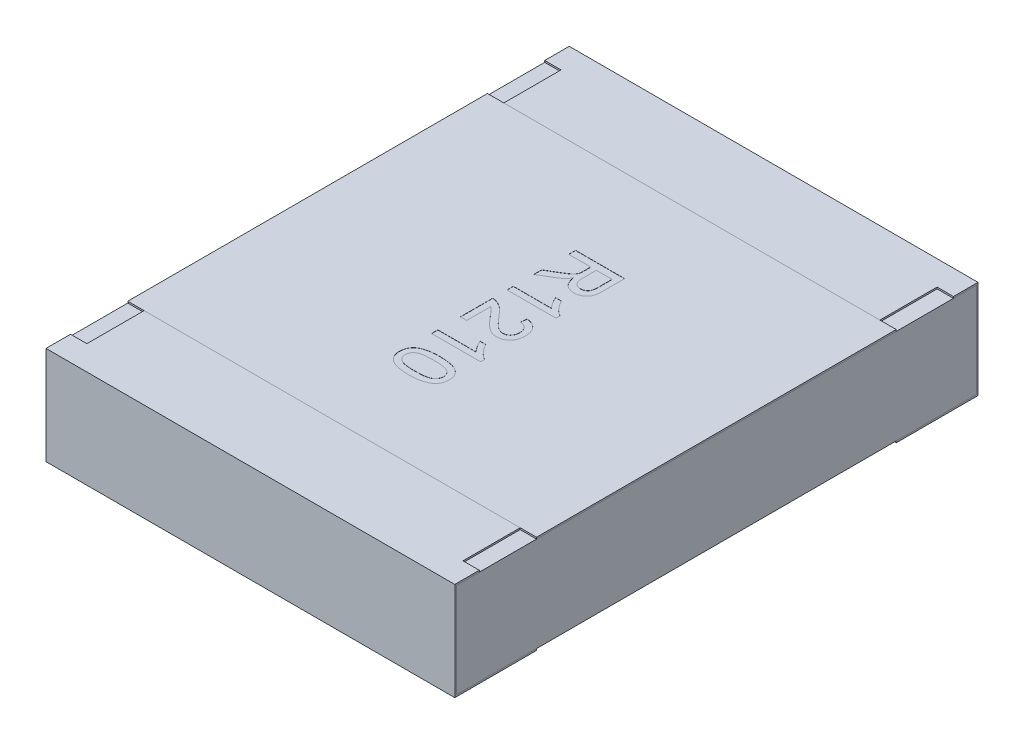
SolidWorks part; units mm, degrees
ref_plane "Front Plane" through (0, 0, 0) normal (0, 0, 1) x (1, 0, 0)
ref_plane "Top Plane" through (0, 0, 0) normal (0, 1, 0) x (1, 0, 0)
ref_plane "Right Plane" through (0, 0, 0) normal (1, 0, 0) x (0, 0, -1)
sketch "Sketch4" plane through (0, 0, 0) normal (1, 0, 0) x (0, 0, -1)
  line L0 (0, 0.1169) -> (0, -0.0721) construction
  line L1 (-1.6, 0) -> (0.3788, 0) construction
  line L2 (-1.6, 0.3) -> (-1.6, -0.3)
  line L3 (-1.6, -0.3) -> (-1.1, -0.3)
  line L4 (-1.1, 0.3) -> (-1.1, 0.29)
  line L5 (-1.1, 0.29) -> (-1.59, 0.29)
  line L6 (-1.59, 0.29) -> (-1.59, -0.29)
  line L7 (-1.59, -0.29) -> (-1.1, -0.29)
  line L8 (-1.1, -0.29) -> (-1.1, -0.3)
  line L9 (-1.1, 0.3) -> (-1.6, 0.3)
  line L10 (1.1, 0.3) -> (1.6, 0.3)
  line L11 (1.1, -0.29) -> (1.1, -0.3)
  line L12 (1.59, -0.29) -> (1.1, -0.29)
  line L13 (1.59, 0.29) -> (1.59, -0.29)
  line L14 (1.1, 0.29) -> (1.59, 0.29)
  line L15 (1.1, 0.3) -> (1.1, 0.29)
  line L16 (1.6, -0.3) -> (1.1, -0.3)
  line L17 (1.6, 0.3) -> (1.6, -0.3)
  dimension "LENGTH" = 1.6
  dimension "HEIGHT" = 0.6
  dimension "END CAP TOP LENGTH" = 0.5
  dimension "END CAP BOTTOM LENGTH" = 0.5
  dimension "D5" = 0.01
  dimension "D6" = 0.01
extrude "Boss-Extrude2" add sketch "Sketch4" along normal mid plane 2.5
sketch "Sketch5" plane through (0, 0, 0) normal (1, 0, 0) x (0, 0, -1)
  line L1 (-1.59, 0.29) -> (1.59, 0.29)
  line L2 (-1.59, 0.29) -> (-1.59, -0.29)
  line L3 (-1.59, -0.29) -> (1.59, -0.29)
  line L4 (1.59, 0.29) -> (1.59, -0.29)
extrude "Boss-Extrude3" add sketch "Sketch5" along normal up to surface and the other way up to surface separate body
sketch "Sketch6" plane through (0, 0.3, 0) normal (0, 1, 0) x (1, 0, 0)
  line L0 (-1.25, 1.6) -> (-1.25, 1.1) construction
  line L1 (-1.25, 1.45) -> (-1.15, 1.45)
  line L2 (-1.25, 1.45) -> (-1.25, 1.1)
  line L3 (-1.25, 1.1) -> (-1.15, 1.1)
  line L4 (-1.15, 1.45) -> (-1.15, 1.1)
  line L5 (1.25, 1.1) -> (-1.25, 1.1) construction
  line L6 (0, 0.0345) -> (0, -0.0345) construction
  line L7 (-0.0325, 0) -> (0.03, 0) construction
  line L8 (1.25, 1.45) -> (1.25, 1.1)
  line L9 (1.25, 1.1) -> (1.15, 1.1)
  line L10 (1.15, 1.45) -> (1.15, 1.1)
  line L11 (1.25, 1.45) -> (1.15, 1.45)
  line L12 (1.25, -1.45) -> (1.15, -1.45)
  line L13 (1.25, -1.45) -> (1.25, -1.1)
  line L14 (1.25, -1.1) -> (1.15, -1.1)
  line L15 (1.15, -1.45) -> (1.15, -1.1)
  line L16 (-1.25, -1.45) -> (-1.15, -1.45)
  line L17 (-1.25, -1.45) -> (-1.25, -1.1)
  line L18 (-1.25, -1.1) -> (-1.15, -1.1)
  line L19 (-1.15, -1.45) -> (-1.15, -1.1)
  dimension "TOP CUT WIDTH" = 0.1
  dimension "TOP CUT LENGTH" = 0.35
extrude "Cut-Extrude1" cut sketch "Sketch6" against normal up to surface (0.01 mm away) up to face at (0, 0.29, 0)
sketch "Sketch7" plane through (0, 0.29, 0) normal (0, 1, 0) x (1, 0, 0)
  line L1 (-1.25, 1.1) -> (1.25, 1.1)
  line L2 (-1.25, 1.1) -> (-1.25, -1.1)
  line L3 (-1.25, -1.1) -> (1.25, -1.1)
  line L4 (1.25, 1.1) -> (1.25, -1.1)
  line L5 (1.15, -1.1) -> (-1.15, -1.1) construction
  line L6 (1.15, 1.1) -> (-1.15, 1.1) construction
  line L7 (-1.25, -1.59) -> (-1.25, 1.59) construction
  line L8 (1.25, 1.59) -> (1.25, -1.59) construction
extrude "Boss-Extrude4" add sketch "Sketch7" along normal up to surface (0.01 mm away) separate body up to face at (0, 0.3, -1.4)
sketch "Sketch13" plane through (0, 0.3, 0) normal (0, 1, 0) x (1, 0, 0)
  line L0 (-0.15, 0.5735) -> (-0.15, -0.5735) construction
  line L1 (0, 0) -> (-0.15, 0) construction
  text T0 "R1210" font "Arial" height 0.3
  dimension "D1" = 0.15
extrude "TEXT1210" cut sketch "Sketch13" against normal blind 0.001
